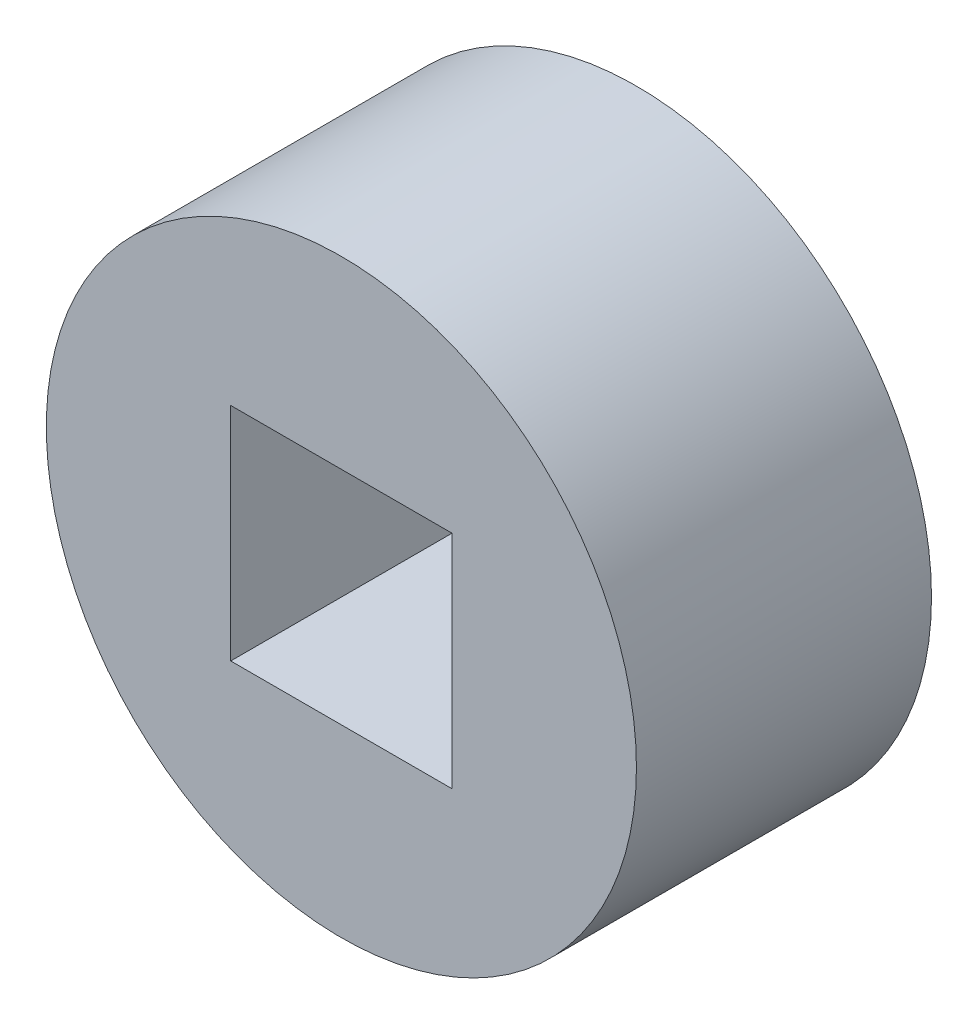
SolidWorks part; units mm, degrees
ref_plane "前视基准面" through (0, 0, 0) normal (0, 0, 1) x (1, 0, 0)
ref_plane "上视基准面" through (0, 0, 0) normal (0, 1, 0) x (1, 0, 0)
ref_plane "右视基准面" through (0, 0, 0) normal (1, 0, 0) x (0, 0, -1)
other "Configuration Table"
sketch "草图1" plane through (0, 0, 0) normal (0, 0, 1) x (1, 0, 0)
  line L1 (-1.5, -1.5) -> (1.5, -1.5)
  line L2 (-1.5, -1.5) -> (-1.5, 1.5)
  line L3 (-1.5, 1.5) -> (1.5, 1.5)
  line L4 (1.5, -1.5) -> (1.5, 1.5)
  line L5 (0, 1.5) -> (0, -1.5) construction
  line L6 (-1.5, 0) -> (1.5, 0) construction
  circle A0 centre (0, 0) radius 4
  dimension "D1" = 3
  dimension "D2" = 3
extrude "凸台-拉伸1" add sketch "草图1" along normal blind 4
